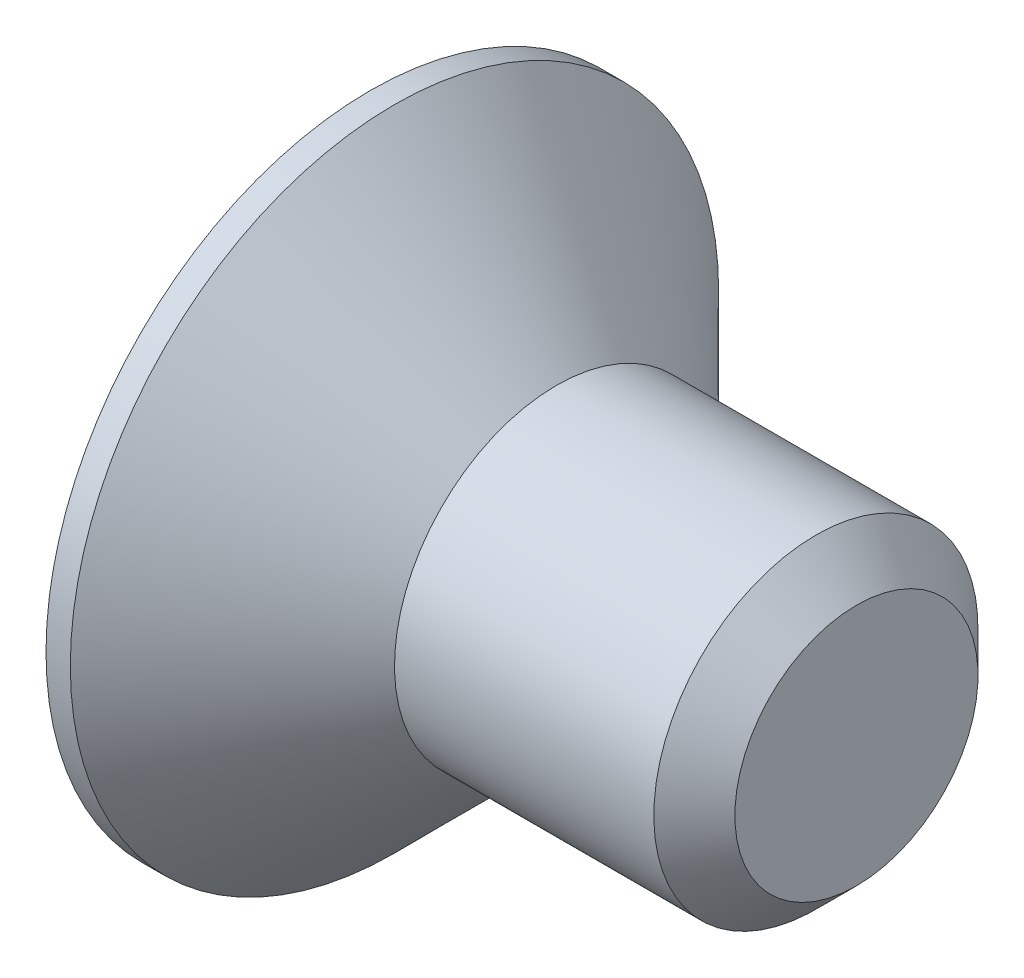
SolidWorks part; units mm, degrees
ref_plane "Plan de face" through (0, 0, 0) normal (0, 0, 1) x (1, 0, 0)
ref_plane "Plan de dessus" through (0, 0, 0) normal (0, 1, 0) x (1, 0, 0)
ref_plane "Plan de droite" through (0, 0, 0) normal (1, 0, 0) x (0, 0, -1)
sketch "Esquisse1" plane through (0, 0, 0) normal (0, 0, 1) x (1, 0, 0)
  line L0 (0, 0) -> (0, 4)
  line L1 (0, 4) -> (0.3, 4)
  line L2 (0.3, 4) -> (2.3, 2)
  line L3 (2.3, 2) -> (6, 2)
  line L4 (6, 2) -> (6, 0)
  line L5 (6, 0) -> (0, 0) construction
  line L6 (0, 0) -> (6, 0)
  dimension "D1" = 2.3
  dimension "D2" = 6
  dimension "D3" = 4
  dimension "D4" = 8
  dimension "D5" = 45
revolve "Révolution1" add sketch "Esquisse1" angle 360 about L5
chamfer "Chanfrein1" distance 0.5 angle 45 1 edges at (6, 2, 0)
sketch "Esquisse2" plane through (0, 0, 0) normal (-1, 0, 0) x (0, 0, 1)
  line L1 (0, 1.4434) -> (-1.25, 0.7217)
  line L2 (-1.25, 0.7217) -> (-1.25, -0.7217)
  line L3 (-1.25, -0.7217) -> (0, -1.4434)
  line L4 (0, -1.4434) -> (1.25, -0.7217)
  line L5 (1.25, -0.7217) -> (1.25, 0.7217)
  line L6 (1.25, 0.7217) -> (0, 1.4434)
  circle A0 centre (0, 0) radius 1.25 construction
  dimension "D1" = 2.5
extrude "Enlèv. mat.-Extru.1" cut sketch "Esquisse2" against normal blind 1.8
